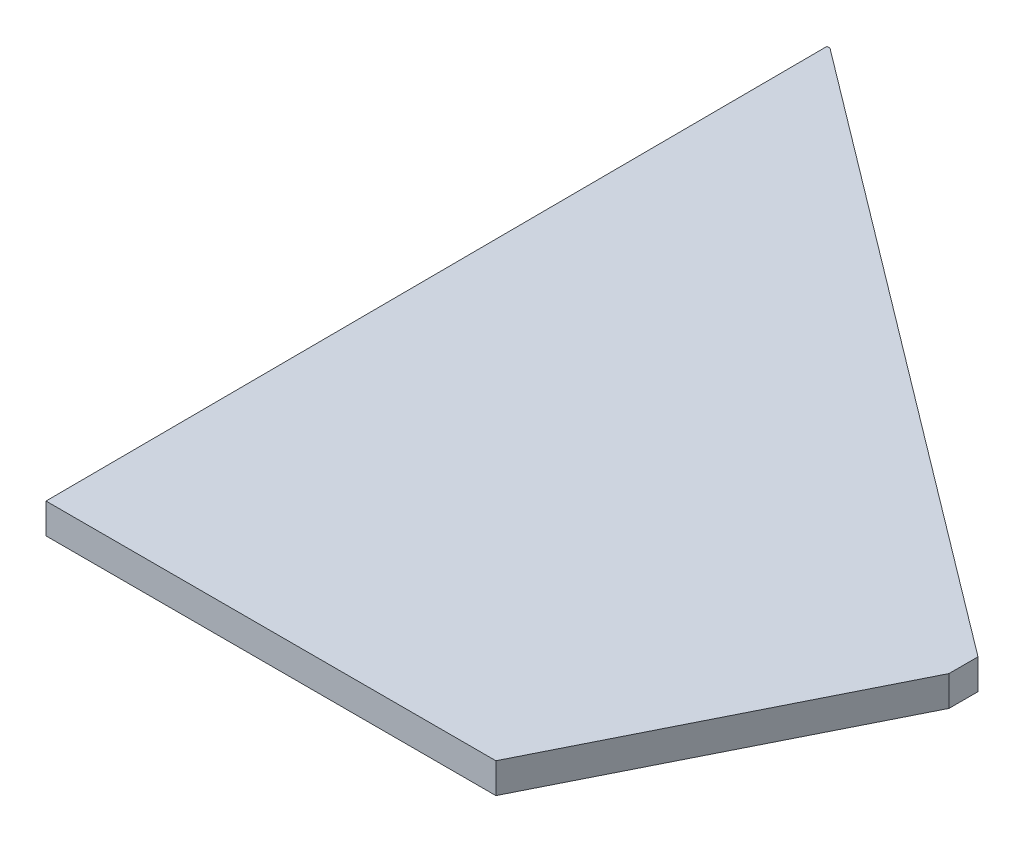
SolidWorks part; units mm, degrees
ref_plane "Plan de face" through (0, 0, 0) normal (0, 0, 1) x (1, 0, 0)
ref_plane "Plan de dessus" through (0, 0, 0) normal (0, 1, 0) x (1, 0, 0)
ref_plane "Plan de droite" through (0, 0, 0) normal (1, 0, 0) x (0, 0, -1)
sketch "Esquisse1" plane through (0, 0, 0) normal (0, 1, 0) x (1, 0, 0)
  line L0 (39.784, 20) -> (39.784, 21.9201)
  line L1 (39.784, 21.9201) -> (-0.016, 51.9201)
  line L2 (-0.016, 51.9201) -> (-0.216, 51.9201)
  line L3 (-0.216, 51.9201) -> (0, 0)
  line L4 (0, 0) -> (29.784, 0)
  line L5 (29.784, 0) -> (39.784, 20)
  point P6 (0, 0)
extrude "Boss.-Extru.1" add sketch "Esquisse1" along normal blind 2
